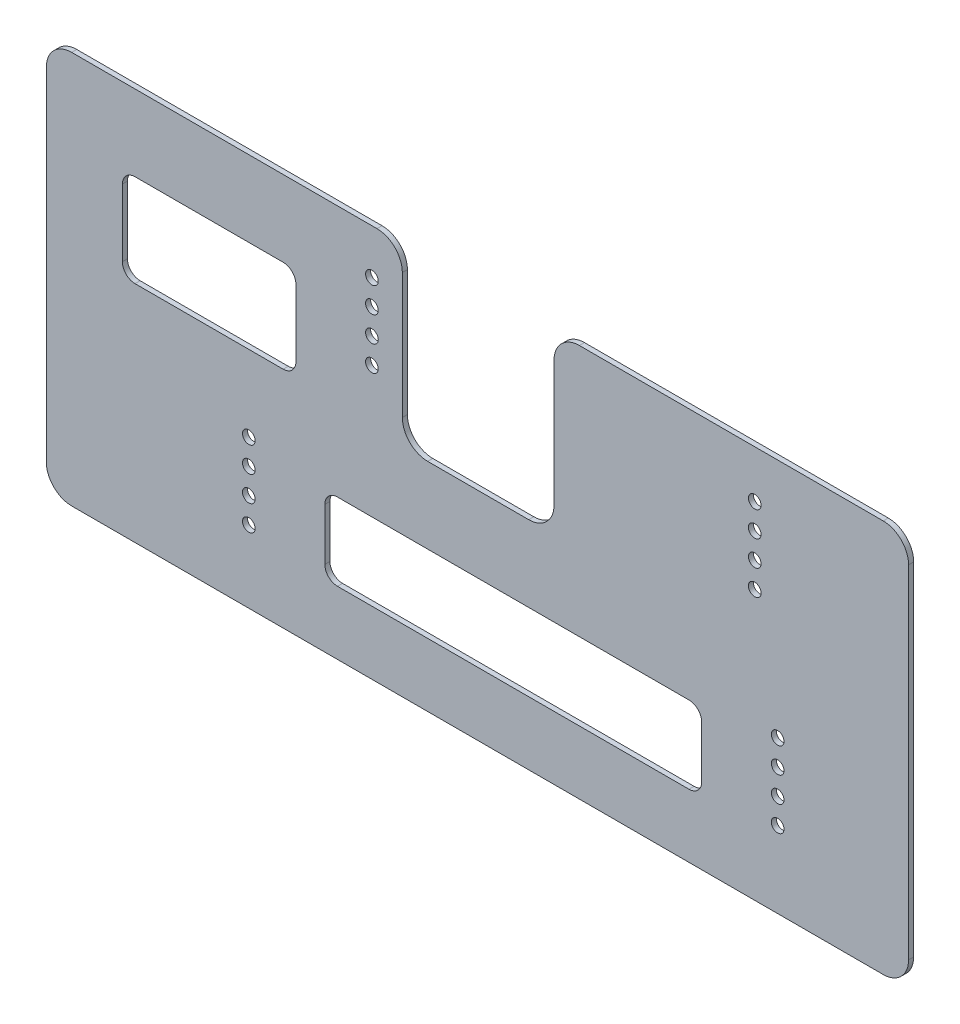
SolidWorks part; units mm, degrees
ref_plane "Front Plane" through (0, 0, 0) normal (0, 0, 1) x (1, 0, 0)
ref_plane "Top Plane" through (0, 0, 0) normal (0, 1, 0) x (1, 0, 0)
ref_plane "Right Plane" through (0, 0, 0) normal (1, 0, 0) x (0, 0, -1)
sketch "Sketch1" plane through (0, 0, 0) normal (0, 0, 1) x (1, 0, 0)
  line L0 (269.9, -1100) -> (269.9, 0) construction
  line L1 (610.1, -1100) -> (269.9, -1100)
  line L2 (610.1, -1100) -> (610.1, -945)
  line L3 (610.1, -945) -> (269.9, -945)
  line L4 (269.9, -1100) -> (269.9, -945)
  dimension "D1" = 155
extrude "Boss-Extrude1" add sketch "Sketch1" along normal blind 2 contours L3 L4 L1 L2
sketch "Sketch2" plane through (0, 0, 2) normal (0, 0, 1) x (1, 0, 0)
  circle A0 centre (558.4495, -1039.94) radius 2.5
  circle A1 centre (349.7846, -1041.526) radius 2.5
  circle A2 centre (398.3545, -962.7153) radius 2.5
  circle A3 centre (549.4056, -963.766) radius 2.5
  dimension "D1" = 5
extrude "Cut-Extrude1" cut sketch "Sketch2" against normal through all
pattern_linear "LPattern1" count 4 spacing 10 along (0, -1, 0) of "Cut-Extrude1"
sketch "Sketch3" plane through (0, 0, 2) normal (0, 0, 1) x (1, 0, 0)
  line L1 (470.2166, -974.5127) -> (410.354, -974.5127)
  line L2 (470.2166, -974.5127) -> (470.2166, -954.0127)
  line L3 (470.2166, -954.0127) -> (410.354, -954.0127)
  line L4 (410.354, -974.5127) -> (410.354, -954.0127)
extrude "Cut-Extrude2" cut sketch "Sketch3" against normal through all
pattern_linear "LPattern2" count 5 spacing 10 along (0, 1, 0) of "Cut-Extrude2"
sketch "Sketch4" plane through (0, 0, 2) normal (0, 0, 1) x (1, 0, 0)
  line L0 (610.1, -945) -> (269.9, -945) construction
  line L1 (470.2166, -954.0127) -> (410.354, -954.0127)
  line L2 (470.2166, -954.0127) -> (470.2166, -945)
  line L3 (470.2166, -945) -> (410.354, -945)
  line L4 (410.354, -954.0127) -> (410.354, -945)
  line L5 (410.354, -954.0127) -> (410.354, -974.5127) construction
extrude "Cut-Extrude3" cut sketch "Sketch4" against normal through all
fillet "Fillet1" radius 10 4 edges at (470.2166, -945, 1) (410.354, -945, 1) (470.2166, -1014.5127, 1) (410.354, -1014.5127, 1)
fillet "Fillet2" radius 10 4 edges at (610.1, -945, 1) (610.1, -1100, 1) (269.9, -945, 1) (269.9, -1100, 1)
sketch "Sketch5" plane through (0, 0, 2) normal (0, 0, 1) x (1, 0, 0)
  line L0 (558.4495, -1069.94) -> (558.4495, -1039.94) construction
  line L1 (523.4495, -1075) -> (384.7846, -1075)
  line L2 (528.4495, -1070) -> (528.4495, -1049.5127)
  line L3 (523.4495, -1044.5127) -> (384.7846, -1044.5127)
  line L4 (379.7846, -1070) -> (379.7846, -1049.5127)
  line L5 (363.3545, -1011.526) -> (304.9, -1011.526)
  line L6 (368.3545, -1006.526) -> (368.3545, -980)
  line L7 (363.3545, -975) -> (304.9, -975)
  line L8 (299.9, -1006.526) -> (299.9, -980)
  line L9 (349.7846, -1071.526) -> (349.7846, -1041.526) construction
  line L10 (349.7846, -1056.526) -> (379.7846, -1056.526) construction
  line L11 (558.4495, -1054.94) -> (528.4495, -1054.94) construction
  line L12 (600.1, -1100) -> (279.9, -1100) construction
  line L13 (420.354, -1014.5127) -> (460.2166, -1014.5127) construction
  line L14 (398.3545, -992.7153) -> (398.3545, -962.7153) construction
  line L15 (269.9, -1090) -> (269.9, -955) construction
  line L16 (400.354, -945) -> (279.9, -945) construction
  arc A0 (304.9, -1011.526) -> (299.9, -1006.526) centre (304.9, -1006.526) cw
  arc A1 (299.9, -980) -> (304.9, -975) centre (304.9, -980) cw
  arc A2 (363.3545, -975) -> (368.3545, -980) centre (363.3545, -980) cw
  arc A3 (368.3545, -1006.526) -> (363.3545, -1011.526) centre (363.3545, -1006.526) cw
  arc A4 (384.7846, -1075) -> (379.7846, -1070) centre (384.7846, -1070) cw
  arc A5 (379.7846, -1049.5127) -> (384.7846, -1044.5127) centre (384.7846, -1049.5127) cw
  arc A6 (528.4495, -1049.5127) -> (523.4495, -1044.5127) centre (523.4495, -1049.5127) ccw
  arc A7 (528.4495, -1070) -> (523.4495, -1075) centre (523.4495, -1070) cw
  dimension "D1" = 5
  dimension "D2" = 30
  dimension "D3" = 25
  dimension "D4" = 30
  dimension "D5" = 30
  dimension "D6" = 30
  dimension "D7" = 30
  dimension "D8" = 30
extrude "Cut-Extrude4" cut sketch "Sketch5" against normal through all
